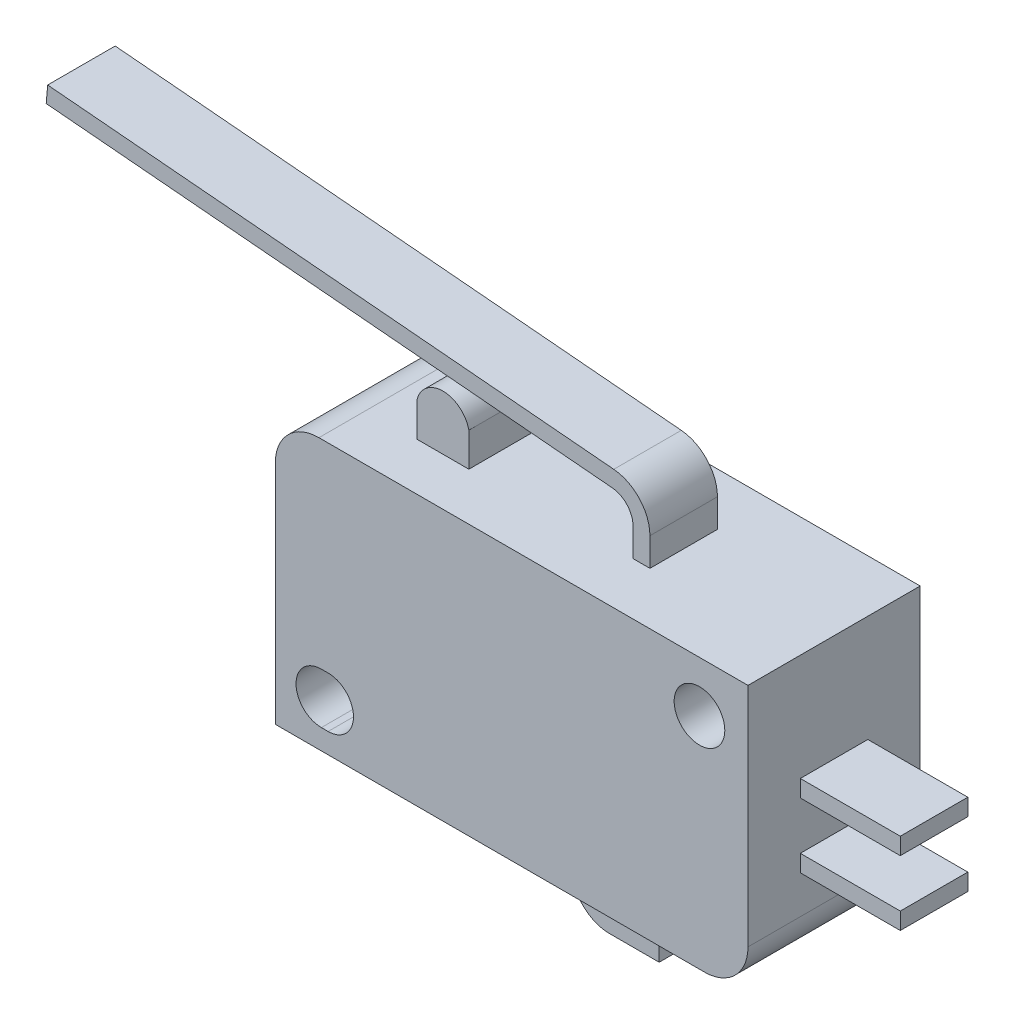
SolidWorks part; units mm, degrees
ref_plane "Front Plane" through (0, 0, 0) normal (0, 0, 1) x (1, 0, 0)
ref_plane "Top Plane" through (0, 0, 0) normal (0, 1, 0) x (1, 0, 0)
ref_plane "Right Plane" through (0, 0, 0) normal (1, 0, 0) x (0, 0, -1)
sketch "Sketch1" plane through (0, 0, 0) normal (0, 0, 1) x (1, 0, 0)
  line L0 (0, 0) -> (25.4182, 0)
  line L1 (28, 2.5818) -> (28, 16)
  line L2 (28, 16) -> (2.5818, 16)
  line L3 (0, 13.4182) -> (0, 0)
  arc A0 (25.4182, 0) -> (28, 2.5818) centre (25.4182, 2.5818) ccw
  arc A1 (2.5818, 16) -> (0, 13.4182) centre (2.5818, 13.4182) ccw
  dimension "D1" = 28
  dimension "D2" = 16
extrude "Boss-Extrude1" add sketch "Sketch1" along normal mid plane 10.2
sketch "Sketch2" plane through (0, 0, 5.1) normal (0, 0, 1) x (1, 0, 0)
  line L0 (2.7261, 2.6983) -> (3.1261, 2.6983) construction
  line L1 (2.7261, 4.1983) -> (3.1261, 4.1983)
  line L2 (2.7261, 1.1983) -> (3.1261, 1.1983)
  arc A0 (2.7261, 4.1983) -> (2.7261, 1.1983) centre (2.7261, 2.6983) ccw
  circle A1 centre (25.1261, 12.9983) radius 1.5
  arc A2 (3.1261, 1.1983) -> (3.1261, 4.1983) centre (3.1261, 2.6983) ccw
  point P4 (2.9261, 2.6983)
  dimension "D1" = 3
  dimension "D2" = 22.2
  dimension "D3" = 10.3
  dimension "D4" = 0.4
extrude "Cut-Extrude1" cut sketch "Sketch2" against normal through all
sketch "Sketch3" plane through (0, 16, 0) normal (0, 1, 0) x (1, 0, 0)
  line L0 (28, 0) -> (2.5818, 0) construction
  line L1 (5.5655, -2.277) -> (8.6409, -2.277)
  line L2 (5.5655, -2.277) -> (5.5655, 2.277)
  line L3 (5.5655, 2.277) -> (8.6409, 2.277)
  line L4 (8.6409, -2.277) -> (8.6409, 2.277)
  line L5 (28, -5.1) -> (28, 5.1) construction
  line L6 (2.5818, -5.1) -> (2.5818, 5.1) construction
extrude "Boss-Extrude2" add sketch "Sketch3" along normal blind 2
sketch "Sketch4" plane through (0, 0, 2.277) normal (0, 0, -1) x (-1, 0, 0)
  line L0 (-8.6409, 18) -> (-5.5655, 18)
  arc A0 (-5.5655, 18) -> (-8.6409, 18) centre (-7.1032, 17.6686) ccw
extrude "Boss-Extrude3" add sketch "Sketch4" along normal up to surface (4.554 mm away) up to face at (7.1032, 17, -2.277)
sketch "Sketch5" plane through (0, 0, 0) normal (0, 0, 1) x (1, 0, 0)
  line L0 (18.0906, 16) -> (18.0906, 17.6733)
  line L1 (28, 16) -> (2.5818, 16) construction
  line L2 (16.8617, 19.015) -> (-16.6769, 21.9636)
  line L3 (15.4703, 0) -> (15.4703, -1.7069)
  line L4 (0, 0) -> (25.4182, 0) construction
  line L5 (16.6998, -2.9364) -> (19.6385, -2.9364)
  line L6 (28, 9.6739) -> (33.9231, 9.6739)
  line L7 (28, 2.5818) -> (28, 16) construction
  line L8 (28, 5.8335) -> (33.9231, 5.8335)
  arc A0 (18.0906, 17.6733) -> (16.8617, 19.015) centre (16.7438, 17.6733) ccw
  arc A1 (15.4703, -1.7069) -> (16.6998, -2.9364) centre (16.6998, -1.7069) ccw
  dimension "D1" = 50.6
  dimension "D2" = 24.9
extrude "Extrude-Thin1" add sketch "Sketch5" along normal mid plane 4 thin
